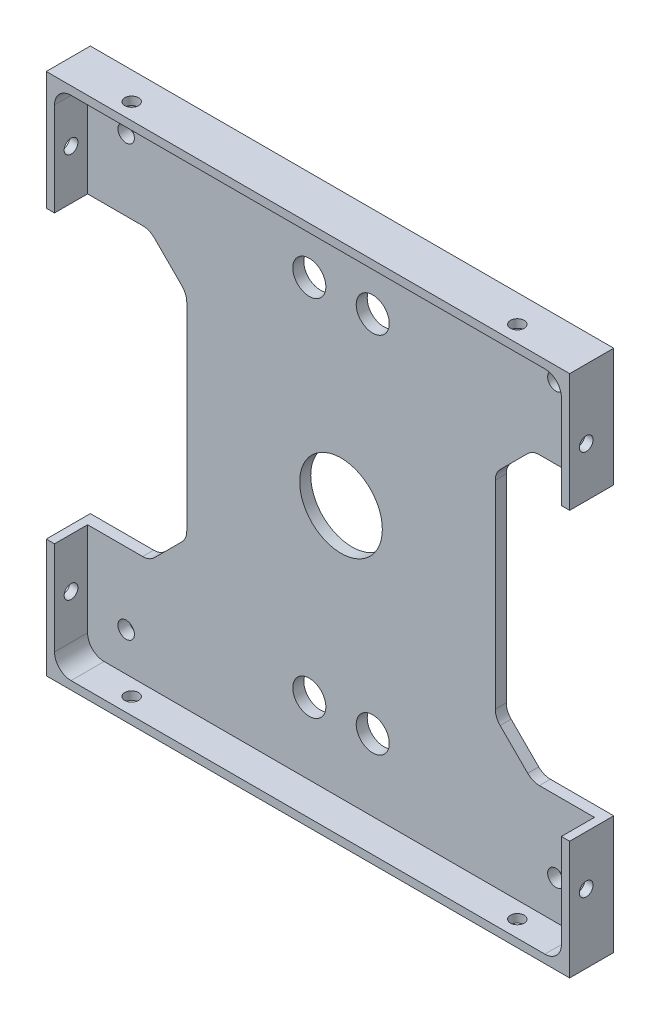
SolidWorks part; units mm, degrees
material "6061-T6 (SS)"
ref_plane "Front" through (0, 0, 0) normal (0, 0, 1) x (1, 0, 0)
ref_plane "Top" through (0, 0, 0) normal (0, 1, 0) x (1, 0, 0)
ref_plane "Right" through (0, 0, 0) normal (1, 0, 0) x (0, 0, -1)
sketch "Sketch1" plane through (0, 0, 0) normal (0, 0, 1) x (1, 0, 0)
  line L1 (-48, -48) -> (48, -48)
  line L2 (-48, -48) -> (-48, 48)
  line L3 (-48, 48) -> (48, 48)
  line L4 (48, -48) -> (48, 48)
  line L5 (-48, -48) -> (48, 48) construction
  line L6 (-48, 48) -> (48, -48) construction
  point P0 (0, 0)
  dimension "D1" = 96
  dimension "D2" = 96
extrude "Boss-Extrude1" add sketch "Sketch1" along normal blind 8
sketch "Sketch16" plane through (0, 0, 0) normal (0, 0, -1) x (-1, 0, 0)
  line L1 (-47.5, -47.5) -> (47.5, -47.5)
  line L2 (-47.5, -47.5) -> (-47.5, 47.5)
  line L3 (-47.5, 47.5) -> (47.5, 47.5)
  line L4 (47.5, -47.5) -> (47.5, 47.5)
  line L5 (-47.5, -47.5) -> (47.5, 47.5) construction
  line L6 (-47.5, 47.5) -> (47.5, -47.5) construction
  point P0 (0, 0)
  dimension "D1" = 95
  dimension "D2" = 95
sketch "Sketch2" plane through (0, 0, 8) normal (0, 0, 1) x (1, 0, 0)
  line L1 (46, -46) -> (-46, -46)
  line L2 (46, -46) -> (46, 46)
  line L3 (46, 46) -> (-46, 46)
  line L4 (-46, -46) -> (-46, 46)
  line L5 (46, -46) -> (-46, 46) construction
  line L6 (46, 46) -> (-46, -46) construction
  point P0 (0, 0)
  dimension "D1" = 92
  dimension "D2" = 92
extrude "Component Platform" cut sketch "Sketch2" against normal blind 6
sketch "Sketch3" plane through (0, 0, 2) normal (0, 0, 1) x (1, 0, 0)
  line L1 (-33.8787, -25.1213) -> (-28.8787, -20.1213)
  line L2 (-33.8787, 25.1213) -> (-28.8787, 20.1213)
  line L3 (-28, -18) -> (-28, 18)
  line L4 (-48, -26) -> (-36, -26)
  line L7 (-48, 48) -> (-48, -48) construction
  line L8 (0, -56.7987) -> (0, 73.4321) construction
  line L9 (46, -46) -> (-57.8147, 57.8147) construction
  line L18 (46, 46) -> (-68.5705, -68.5705) construction
  line L23 (-48, 26) -> (-36, 26)
  line L26 (-48, -26) -> (-48, 26)
  line L28 (-48, -48) -> (48, -48) construction
  line L29 (48, -26) -> (48, 26)
  line L30 (48, 26) -> (36, 26)
  line L31 (33.8787, 25.1213) -> (28.8787, 20.1213)
  line L32 (28, -18) -> (28, 18)
  line L33 (33.8787, -25.1213) -> (28.8787, -20.1213)
  line L34 (48, -26) -> (36, -26)
  arc A3 (-28.8787, -20.1213) -> (-28, -18) centre (-31, -18) ccw
  arc A4 (-28.8787, 20.1213) -> (-28, 18) centre (-31, 18) cw
  arc A13 (-33.8787, -25.1213) -> (-36, -26) centre (-36, -23) cw
  arc A15 (-33.8787, 25.1213) -> (-36, 26) centre (-36, 23) ccw
  arc A17 (33.8787, 25.1213) -> (36, 26) centre (36, 23) cw
  arc A18 (28.8787, 20.1213) -> (28, 18) centre (31, 18) ccw
  arc A19 (28.8787, -20.1213) -> (28, -18) centre (31, -18) cw
  arc A20 (33.8787, -25.1213) -> (36, -26) centre (36, -23) ccw
  point P0 (-48, 0)
  point P37 (-48, 0)
  dimension "D2" = 3
  dimension "D3" = 3
  dimension "D4" = 20
  dimension "D6" = 3
  dimension "D7" = 3
  dimension "D8" = 135
  dimension "D5" = 52
  dimension "D9" = 135
  dimension "D10" = 12
  dimension "D11" = 12
  dimension "D12" = 48
extrude "Cable Slots" cut sketch "Sketch3" against normal mid plane 12
sketch "Sketch4" plane through (0, 0, 2) normal (0, 0, 1) x (1, 0, 0)
  circle A0 centre (0, 0) radius 7.5
  dimension "D1" = 15
extrude "Center Mass Cut" cut sketch "Sketch4" against normal blind 6
ref_plane "Center Y-Plane" through (0, 0, 0) normal (1, 0, 0) x (0, 0, -1)
ref_plane "Center X-Plane" through (0, 0, 0) normal (0, -1, 0) x (-1, 0, 0)
fillet "Inner Corner Fillets" radius 3 4 edges at (46, -46, 5) (-46, -46, 5) (46, 46, 5) (-46, 46, 5)
sketch "Sketch7" plane through (0, 0, 2) normal (0, 0, 1) x (1, 0, 0)
  line L1 (39, -39) -> (-39, -39)
  line L2 (39, -39) -> (39, 39)
  line L3 (39, 39) -> (-39, 39)
  line L4 (-39, -39) -> (-39, 39)
  line L5 (39, -39) -> (-39, 39) construction
  line L6 (39, 39) -> (-39, -39) construction
  point P0 (0, 0)
  dimension "D1" = 78
  dimension "D2" = 78
sketch "Sketch8" plane through (0, -48, 0) normal (0, -1, 0) x (-1, 0, 0)
  line L0 (48, -5) -> (-48, -5) construction
  line L1 (48, -8) -> (48, 0) construction
  line L2 (-48, -8) -> (-48, 0) construction
  line L3 (48, -8) -> (-48, -8) construction
  dimension "D1" = 3
sketch "Sketch9" plane through (48, 0, 0) normal (1, 0, 0) x (0, 0, -1)
  line L0 (-5, 48) -> (-5, -48) construction
  line L1 (-8, 48) -> (0, 48) construction
  line L2 (-8, -48) -> (0, -48) construction
  line L3 (-8, 26) -> (-8, 48) construction
  dimension "D1" = 3
hole_wizard "Tap Drill for M3x0.5 Tap1" positions "Sketch10" profile "Sketch11" hole size "M3x0.5" standard "ANSI Metric" end condition up to next
sketch "Sketch10" plane through (0, -48, 0) normal (0, -1, 0) x (-1, 0, 0)
  line L0 (48, -5) -> (-48, -5) construction
  point P0 (35, -5)
  point P4 (-35, -5)
  dimension "D1" = 70
  dimension "D2" = 35
sketch "Sketch11" plane through (-35, -48, 5) normal (1, 0, 0) x (0, 0, -1)
  line L0 (0, 0) -> (0, 2)
  line L1 (0, 2) -> (1.25, 2)
  line L2 (1.25, 2) -> (1.25, 0)
  line L5 (1.25, 0) -> (0, 0)
  line L11 (0, -6.35) -> (0, 107.95) construction
  dimension "Thru Hole Dia." = 2.5
  dimension "Thru Hole Depth" = 2
hole_wizard "Tap Drill for M3x0.5 Tap2" positions "Sketch12" profile "Sketch13" hole size "M3x0.5" standard "ANSI Metric" end condition up to next
sketch "Sketch12" plane through (48, 0, 0) normal (1, 0, 0) x (0, 0, -1)
  line L0 (-5, 48) -> (-5, -48) construction
  point P0 (-5, -35)
  point P4 (-5, 35)
  dimension "D1" = 70
  dimension "D2" = 35
sketch "Sketch13" plane through (48, -35, 5) normal (0, 1, 0) x (0, 0, -1)
  line L0 (0, 0) -> (0, 2)
  line L1 (0, 2) -> (1.25, 2)
  line L2 (1.25, 2) -> (1.25, 0)
  line L5 (1.25, 0) -> (0, 0)
  line L11 (0, -6.35) -> (0, 107.95) construction
  dimension "Thru Hole Dia." = 2.5
  dimension "Thru Hole Depth" = 2
mirror "Mirror1" about plane through (0, 0, 0) normal (0, -1, 0) of "Tap Drill for M3x0.5 Tap1"
mirror "Mirror2" about plane through (0, 0, 0) normal (1, 0, 0) of "Tap Drill for M3x0.5 Tap2"
hole_wizard "Ø3.0mm Dowel Hole3" positions "Sketch14" profile "Sketch15" hole size "Ø3.0" standard "ANSI Metric"
sketch "Sketch14" plane through (0, 0, 2) normal (0, 0, 1) x (1, 0, 0)
  point P0 (-39, -39)
  point P3 (39, -39)
  point P6 (39, 39)
  point P9 (-39, 39)
sketch "Sketch15" plane through (-39, -39, 2) normal (1, 0, 0) x (0, -1, 0)
  line L0 (0, 0) -> (0, 10.9013)
  line L1 (0, 10.9013) -> (1.5, 10)
  line L2 (1.5, 10) -> (1.5, 0)
  line L5 (1.5, 0) -> (0, 0)
  line L10 (0, 10.9013) -> (-1.5, 10) construction
  line L11 (0, -6.35) -> (0, 107.95) construction
  dimension "Hole Dia." = 3
  dimension "Hole Depth" = 10
  dimension "Drill Angle" = 118
extrude "Cut-Extrude1" cut sketch "Sketch16" against normal up to next flip side to cut
sketch "Sketch17" plane through (0, 0, 0) normal (0, 0, -1) x (-1, 0, 0)
  circle A0 centre (-5.755, -33) radius 3
  circle A1 centre (5.755, -33) radius 3
  dimension "D1" = 6
extrude "Cut-Extrude3" cut sketch "Sketch17" against normal through all
mirror "Mirror4" about plane through (0, 0, 0) normal (0, -1, 0) of "Cut-Extrude3"
equation "\"MountingBracketXYSideTolerance\"= - 0.5"
